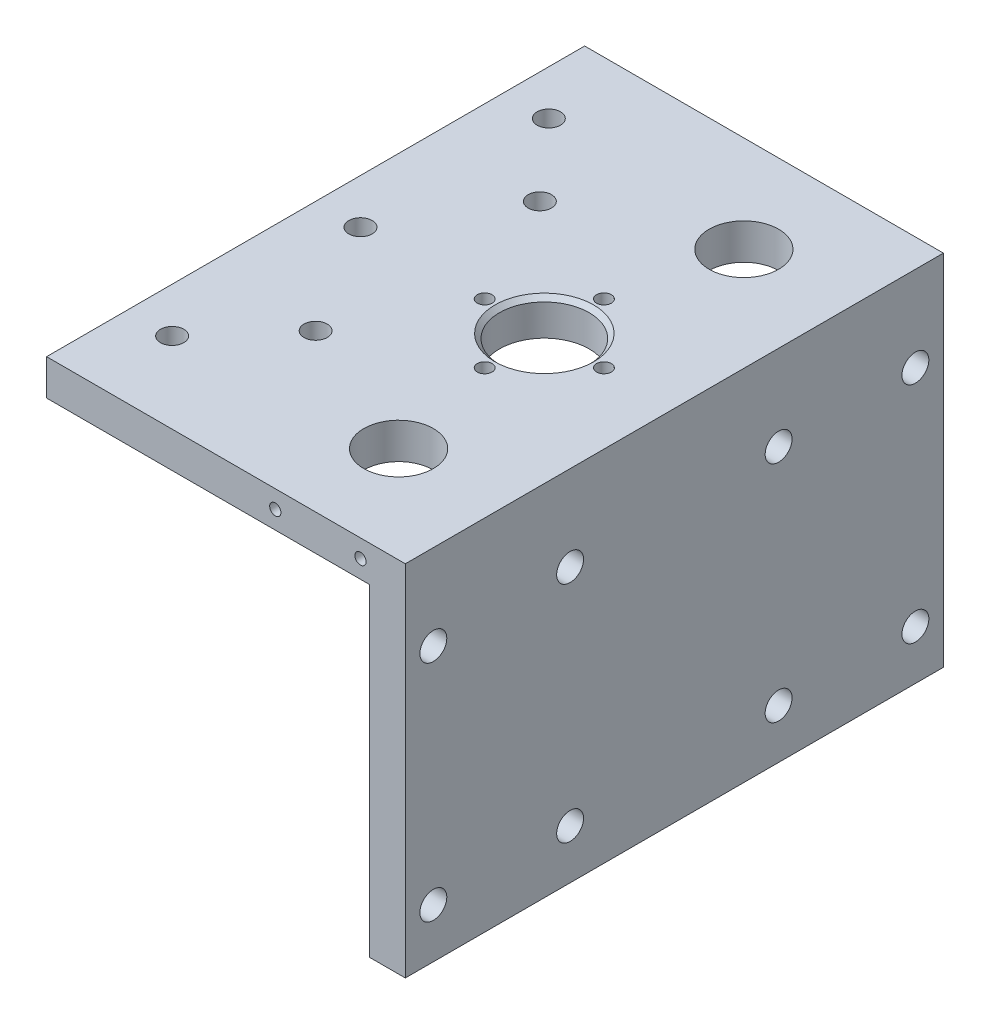
SolidWorks part; units mm, degrees
material "Lega 1060"
ref_plane "Piano frontale" through (0, 0, 0) normal (0, 0, 1) x (1, 0, 0)
ref_plane "Piano superiore" through (0, 0, 0) normal (0, 1, 0) x (1, 0, 0)
ref_plane "Piano destro" through (0, 0, 0) normal (1, 0, 0) x (0, 0, -1)
sketch "Schizzo1" plane through (0, 0, 0) normal (0, 0, 1) x (1, 0, 0)
  line L0 (0, 0) -> (-80, 0)
  line L1 (-80, 0) -> (-80, -8)
  line L2 (-80, -8) -> (-8, -8)
  line L3 (-8, -8) -> (-8, -80)
  line L4 (-8, -80) -> (0, -80)
  line L5 (0, -80) -> (0, 0)
  dimension "D1" = 80
  dimension "D2" = 80
  dimension "D3" = 8
  dimension "D4" = 8
extrude "Estrusione-Estrusione1" add sketch "Schizzo1" along normal blind 120
sketch "Schizzo12" plane through (0, 0, 0) normal (1, 0, 0) x (0, 0, -1)
  line L0 (0, -8) -> (-120, -8) construction
  line L1 (-21.5, 0) -> (-21.5, 40.839) construction
  line L5 (0, -80) -> (0, 0) construction
  line L6 (-120, -80) -> (-120, 0) construction
  line L7 (-120, 0) -> (0, 0) construction
  line L8 (-113.75, -19) -> (9.6992, -19) construction
  line L9 (-113.75, -69) -> (15.4001, -69) construction
  line L10 (-98.5, -47.4454) -> (-98.5, 40.839) construction
  circle A0 centre (-113.75, -19) radius 3
  circle A1 centre (-83.25, -19) radius 3
  circle A6 centre (-36.75, -19) radius 3
  circle A7 centre (-6.25, -19) radius 3
  circle A10 centre (-83.25, -69) radius 3
  circle A11 centre (-113.75, -69) radius 3
  circle A12 centre (-6.25, -69) radius 3
  circle A13 centre (-36.75, -69) radius 3
  dimension "D1" = 6
  dimension "D5" = 30.5
  dimension "D6" = 30.5
  dimension "D7" = 30.5
  dimension "D8" = 30.5
  dimension "D2" = 8
  dimension "D3" = 11
  dimension "D4" = 61
  dimension "D9" = 21.5
  dimension "D10" = 21.5
sketch "Schizzo6" plane through (0, 0, 0) normal (0, 1, 0) x (1, 0, 0)
  line L0 (-23, -0.5808) -> (-23, -110.5835) construction
  line L2 (0, 0) -> (-80, 0) construction
  line L3 (-32.5218, -60) -> (-8.0464, -60) construction
  line L6 (0, -120) -> (-80, -120) construction
  circle A0 centre (-23, -21.5) radius 7.75
  circle A1 centre (-23, -98.5) radius 7.75
  dimension "D2" = 15.5
  dimension "D1" = 15
  dimension "D3" = 21.5
  dimension "D4" = 38.5
extrude "Taglio-Estrusione2" cut sketch "Schizzo6" against normal up to next
sketch "Schizzo7" plane through (0, 0, 0) normal (0, 1, 0) x (1, 0, 0)
  line L0 (-83.5082, -60) -> (3.6289, -60) construction
  line L1 (0, -120) -> (-80, -120) construction
  line L2 (0, 0) -> (-80, 0) construction
  line L3 (-23, -21.5) -> (-23, -98.5) construction
  line L4 (0, -120) -> (0, 0) construction
  circle A0 centre (-29, -60) radius 10
  dimension "D1" = 20
  dimension "D3" = 29
extrude "Taglio-Estrusione3" cut sketch "Schizzo7" against normal up to next
hole_wizard "M4 Tapped Hole1" positions "Schizzo9" profile "Schizzo8" tap size "M4" standard "ISO" end condition through all
sketch "Schizzo9" plane through (0, 0, 0) normal (0, 1, 0) x (1, 0, 0)
  line L0 (-18.4657, -60) -> (-15.7, -60) construction
  line L2 (-29, -57.7684) -> (-29, -66.5063) construction
  circle A2 centre (-29, -60) radius 10 construction
  point P0 (-29, -46.7)
  point P2 (-42.3, -60)
  point P4 (-29, -73.3)
  point P8 (-15.7, -60)
  point P20 (-29, -60)
  dimension "D1" = 26.6
  dimension "D2" = 13.3
  dimension "D3" = 13.3
sketch "Schizzo8" plane through (-29, 0, 46.7) normal (1, 0, 0) x (0, 0, 1)
  line L0 (0, 0) -> (0, 80)
  line L1 (0, 80) -> (1.65, 80)
  line L2 (1.65, 80) -> (1.65, 0)
  line L5 (1.65, 0) -> (0, 0)
  line L11 (0, -6.35) -> (0, 107.95) construction
  dimension "Thread Major Dia." = 3.3
  dimension "Thru Tap Drill Depth" = 80
extrude "Taglio-Estrusione4" cut sketch "Schizzo12" against normal blind 10
sketch "Schizzo14" plane through (0, 0, 0) normal (0, 1, 0) x (1, 0, 0)
  line L0 (-70, 0) -> (-70, -120) construction
  line L1 (0, 0) -> (-80, 0) construction
  line L2 (0, -120) -> (-80, -120) construction
  line L3 (-80, -120) -> (-80, 0) construction
  line L4 (-55, 0) -> (-55, -120) construction
  line L5 (-23, -98.5) -> (-80, -98.5) construction
  line L6 (-80, -60) -> (0, -60) construction
  line L7 (0, -120) -> (0, 0) construction
  line L8 (-23, -21.5) -> (-80, -21.5) construction
  circle A0 centre (-70, -18) radius 2.6
  circle A1 centre (-70, -60) radius 2.6
  circle A2 centre (-70, -102) radius 2.6
  circle A3 centre (-55, -35) radius 2.6
  circle A4 centre (-55, -85) radius 2.6
  dimension "D3" = 5.2
  dimension "D4" = 5.2
  dimension "D5" = 5.2
  dimension "D6" = 5.2
  dimension "D7" = 5.2
  dimension "D1" = 10
  dimension "D2" = 25
  dimension "D8" = 35
  dimension "D9" = 35
  dimension "D10" = 25
  dimension "D11" = 42
  dimension "D12" = 15
extrude "Taglio-Estrusione5" cut sketch "Schizzo14" against normal blind 10
chamfer "Smusso2" distance 1 angle 45 1 edges at (-39, 0, 60)
sketch "Schizzo15" plane through (0, 0, 120) normal (0, 0, 1) x (1, 0, 0)
  line L0 (-80, -4) -> (0, -4) construction
  line L1 (-80, 0) -> (-80, -8) construction
  line L2 (0, -80) -> (0, 0) construction
  point P6 (-10, -4)
  point P7 (-29, -4)
  dimension "D1" = 10
  dimension "D2" = 19
hole_wizard "Foro filettato M3-1" positions "Schizzo17" profile "Schizzo16" tap size "M3" standard "ISO"
sketch "Schizzo17" plane through (0, 0, 120) normal (0, 0, 1) x (1, 0, 0)
  point P0 (-10, -4)
  point P3 (-29, -4)
sketch "Schizzo16" plane through (-10, -4, 120) normal (1, 0, 0) x (0, -1, 0)
  line L0 (0, 0) -> (0, 10.7511)
  line L1 (0, 10.7511) -> (1.25, 10)
  line L2 (1.25, 10) -> (1.25, 0)
  line L5 (1.25, 0) -> (0, 0)
  line L10 (0, 10.7511) -> (-1.25, 10) construction
  line L11 (0, -6.35) -> (0, 107.95) construction
  dimension "Tap Drill Dia." = 2.5
  dimension "Tap Drill Depth" = 10
  dimension "Drill Angle" = 118
cosmetic thread "Filettatura del foro1" parameters "D1"=8, "D2"=3
cosmetic thread "Filettatura del foro2" parameters "D1"=8, "D2"=3
sketch "Sketch1" plane through (0, 0, 0) normal (1, 0, 0) x (0, 0, -1)
  line L0 (0, -80) -> (0, 0) construction
  point P0 (0, -8)
  dimension "D1" = 8
